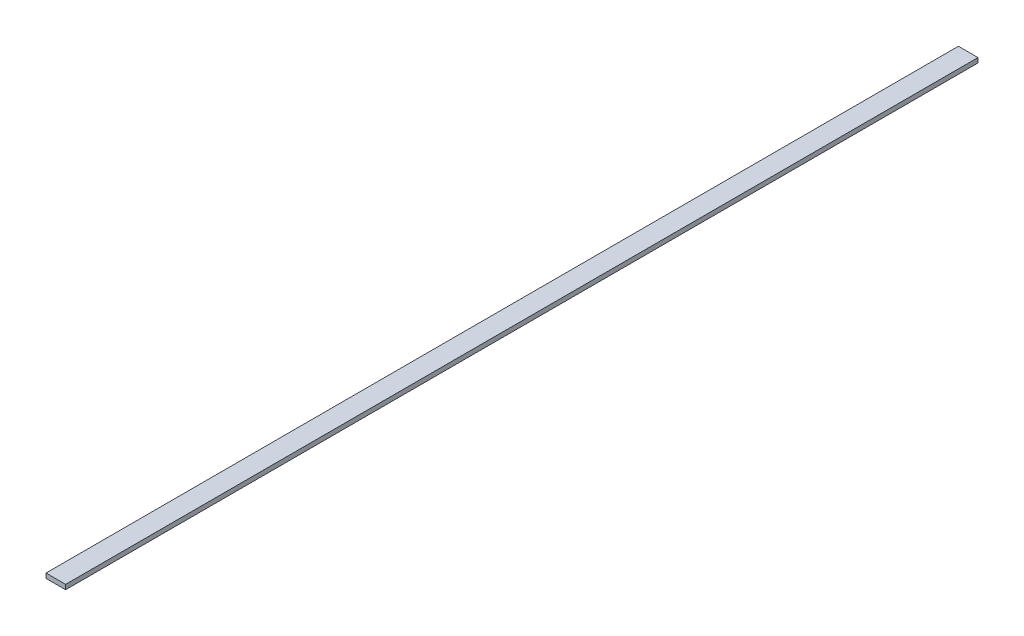
SolidWorks part; units mm, degrees
material "Plain Carbon Steel"
ref_plane "Front Plane" through (0, 0, 0) normal (0, 0, 1) x (1, 0, 0)
ref_plane "Top Plane" through (0, 0, 0) normal (0, 1, 0) x (1, 0, 0)
ref_plane "Right Plane" through (0, 0, 0) normal (1, 0, 0) x (0, 0, -1)
sketch "Sketch1" plane through (0, 0, 0) normal (0, 0, 1) x (1, 0, 0)
  line L1 (0, 0) -> (6.35, 0)
  line L2 (0, 0) -> (0, 1.5189)
  line L3 (0, 1.5189) -> (6.35, 1.5189)
  line L4 (6.35, 0) -> (6.35, 1.5189)
  dimension "D1" = 6.35
  dimension "D2" = 1.5189
extrude "Boss-Extrude1" add sketch "Sketch1" along normal blind 295.4122
